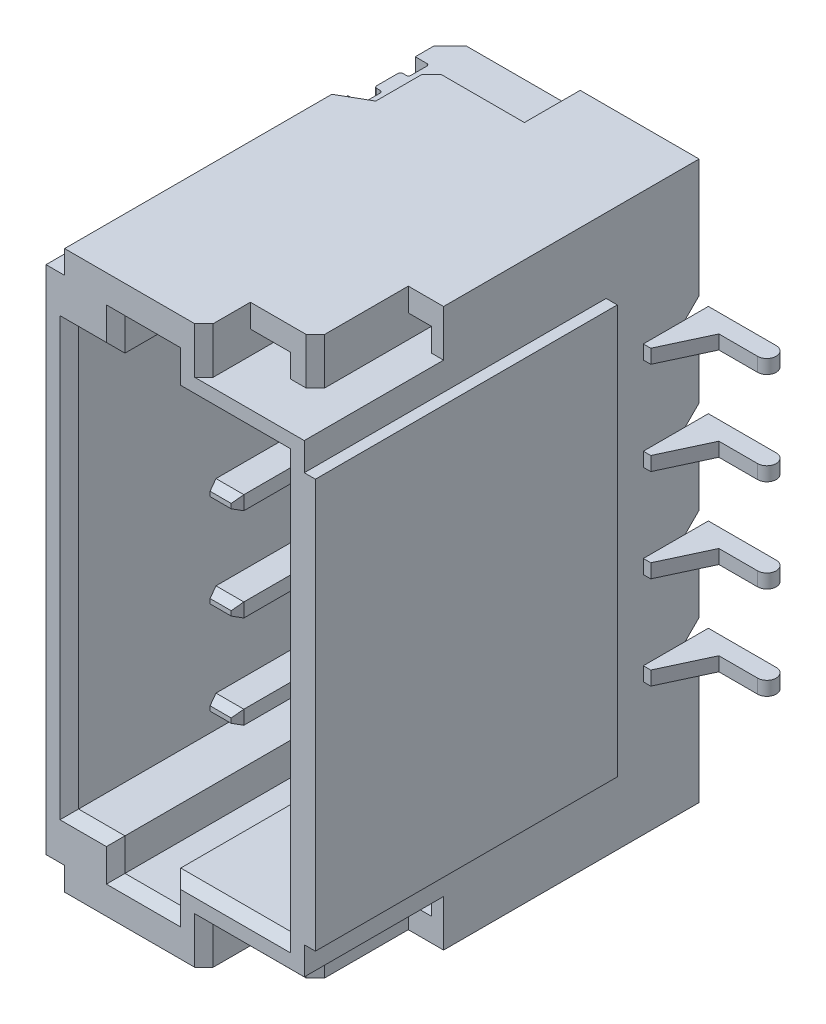
SolidWorks part; units mm, degrees
ref_plane "Front Plane" through (0, 0, 0) normal (0, 0, 1) x (1, 0, 0)
ref_plane "Top Plane" through (0, 0, 0) normal (0, 1, 0) x (1, 0, 0)
ref_plane "Right Plane" through (0, 0, 0) normal (1, 0, 0) x (0, 0, -1)
sketch "Sketch2" plane through (0, 0, 0) normal (0, 1, 0) x (1, 0, 0)
  line L0 (22.6306, -2.3603) -> (22.6306, -1.9103)
  line L1 (22.6306, -1.9103) -> (25.4106, -1.9103)
  line L2 (25.4106, -1.9103) -> (25.4106, -1.6603)
  line L3 (25.4106, -1.6603) -> (26.1406, -1.6603)
  line L4 (26.1406, -1.8603) -> (25.7238, -1.8603)
  line L5 (25.7238, -1.8603) -> (25.4906, -2.3603)
  line L6 (25.4906, -2.3603) -> (22.6306, -2.3603)
  arc A0 (26.1406, -1.8603) -> (26.1406, -1.6603) centre (26.1406, -1.7603) ccw
extrude "Boss-Extrude2" add sketch "Sketch2" along normal blind 0.15 from offset 0.815 separate body contours L6 L0 L1 L2 L3 A0 L4 L5 offset against normal yes
move or copy body "Body-Move/Copy2" bodies to move or copy 124 copy yes number of copies 1 translate (0, -1, 0)
move or copy body "Body-Move/Copy3" bodies to move or copy 124 copy yes number of copies 1 translate (0, 1, 0)
move or copy body "Body-Move/Copy4" bodies to move or copy 126 copy yes number of copies 1 translate (0, 1, 0)
sketch "Sketch3" plane through (0, 0, 0) normal (0, 1, 0) x (1, 0, 0)
  line L0 (22.7306, -2.9603) -> (24.1306, -2.9603)
  line L1 (24.1306, -2.9603) -> (24.1306, -1.8353)
  line L2 (24.1306, -1.8353) -> (23.9556, -1.6603)
  line L3 (23.9556, -1.6603) -> (22.8056, -1.6603)
  line L4 (22.8056, -1.6603) -> (22.6306, -1.8353)
  line L5 (22.6306, -1.8353) -> (22.6306, -2.0353)
  line L6 (22.6306, -2.0353) -> (22.7556, -2.0353)
  line L7 (22.7806, -2.2328) -> (22.7806, -2.0603)
  line L8 (22.6306, -2.7603) -> (22.6306, -2.8603)
  line L9 (22.6306, -2.8603) -> (22.7306, -2.9603)
  line L10 (22.6306, -2.7603) -> (22.7556, -2.7603)
  line L11 (22.7806, -2.7353) -> (22.7806, -2.5628)
  line L12 (22.7181, -2.5378) -> (22.7556, -2.5378)
  line L13 (22.6931, -2.2828) -> (22.6931, -2.5128)
  line L14 (22.7181, -2.2578) -> (22.7556, -2.2578)
  arc A0 (22.7556, -2.7603) -> (22.7806, -2.7353) centre (22.7556, -2.7353) ccw
  arc A1 (22.7806, -2.5628) -> (22.7556, -2.5378) centre (22.7556, -2.5628) ccw
  arc A2 (22.7181, -2.5378) -> (22.6931, -2.5128) centre (22.7181, -2.5128) cw
  arc A3 (22.7556, -2.0353) -> (22.7806, -2.0603) centre (22.7556, -2.0603) cw
  arc A4 (22.7556, -2.2578) -> (22.7806, -2.2328) centre (22.7556, -2.2328) ccw
  arc A5 (22.7181, -2.2578) -> (22.6931, -2.2828) centre (22.7181, -2.2828) ccw
extrude "Boss-Extrude3" add sketch "Sketch3" along normal blind 0.2 from offset 2.26 separate body contours L0 L1 L2 L3 L4 L5 L6 A3 L7 A4 L14 A5 L13 A2 L12 A1 L11 A0 L10 L8 L9
sketch "Sketch4" plane through (0, 0, 0) normal (0, 0, 1) x (1, 0, 0)
  line L0 (25.5306, -3.2409) -> (22.6306, -3.2409)
  line L1 (22.6306, -3.2409) -> (22.6306, 2.7591)
  line L2 (25.5306, 2.7591) -> (22.6306, 2.7591)
  line L3 (25.5306, -3.2409) -> (25.5306, 2.7591)
extrude "Boss-Extrude4" add sketch "Sketch4" along normal blind 4.25 from offset 1.76 separate body
sketch "Sketch5" plane through (22.6306, 0, 0) normal (-1, 0, 0) x (0, 0, 1)
  line L0 (1.7603, 1.4841) -> (1.9103, 1.3341)
  line L1 (1.9103, 1.3341) -> (2.3603, 1.3341)
  line L2 (2.3603, 1.3341) -> (2.3603, 1.1841)
  line L3 (2.3603, 1.1841) -> (1.9103, 1.1841)
  line L4 (1.9103, 1.1841) -> (1.7603, 1.0341)
  line L6 (1.7603, 1.4841) -> (1.7527, 1.4841)
  line L7 (1.7527, 1.4841) -> (1.7527, 1.0341)
  line L8 (1.7527, 1.0341) -> (1.7603, 1.0341)
extrude "Cut-Extrude2" cut sketch "Sketch5" against normal through all
pattern_linear "LPattern1" count 4 spacing 1 along (0, -1, 0) of "Cut-Extrude2"
sketch "Sketch6" plane through (25.5306, 0, 0) normal (1, 0, 0) x (0, 0, -1)
  line L0 (-2.7603, -2.4409) -> (-2.7603, 1.9591)
  line L1 (-2.7603, 1.9591) -> (-6.161, 1.9591)
  line L2 (-6.161, 1.9591) -> (-6.161, -2.4409)
  line L3 (-6.161, -2.4409) -> (-2.7603, -2.4409)
extrude "Cut-Extrude3" cut sketch "Sketch6" against normal blind 0.12 flip side to cut
sketch "Sketch7" plane through (0, 0, 6.01) normal (0, 0, 1) x (1, 0, 0)
  line L0 (22.8806, -2.4909) -> (25.1606, -2.4909)
  line L1 (25.1606, -2.4909) -> (25.1606, 2.0091)
  line L2 (25.1606, 2.0091) -> (22.8806, 2.0091)
  line L3 (22.8806, 2.0091) -> (22.8806, -2.4909)
extrude "Cut-Extrude4" cut sketch "Sketch7" against normal blind 3.2
sketch "Sketch8" plane through (0, 0, 6.01) normal (0, 0, 1) x (1, 0, 0)
  line L0 (23.3806, 2.0091) -> (23.9806, 2.0091)
  line L1 (23.9806, 2.0091) -> (23.9806, 2.3591)
  line L2 (23.9806, 2.3591) -> (23.3806, 2.3591)
  line L3 (23.3806, 2.3591) -> (23.3806, 2.0091)
  line L4 (23.3806, -2.4909) -> (23.9806, -2.4909)
  line L5 (23.9806, -2.4909) -> (23.9806, -2.8409)
  line L6 (23.9806, -2.8409) -> (23.3806, -2.8409)
  line L7 (23.3806, -2.8409) -> (23.3806, -2.4909)
extrude "Cut-Extrude6" cut sketch "Sketch8" against normal blind 2.6
chamfer "Chamfer1" distance 0.1 angle 45 12 edges at (22.8806, -0.2409, 6.01) (23.1306, -2.4909, 6.01) (23.3806, -2.6659, 6.01) (23.6806, -2.8409, 6.01) (23.9806, -2.6659, 6.01) (24.5706, -2.4909, 6.01) (25.1606, -0.2409, 6.01) (24.5706, 2.0091, 6.01) (23.9806, 2.1841, 6.01) (23.6806, 2.3591, 6.01) (23.3806, 2.1841, 6.01) (23.1306, 2.0091, 6.01)
sketch "Sketch9" plane through (0, 0, 0) normal (0, 1, 0) x (1, 0, 0)
  line L0 (23.3606, -2.8103) -> (23.6606, -2.8103)
  line L1 (23.6606, -2.8103) -> (23.6606, -4.9103)
  line L2 (23.6606, -4.9103) -> (23.6242, -5.0103)
  line L3 (23.6242, -5.0103) -> (23.397, -5.0103)
  line L4 (23.397, -5.0103) -> (23.3606, -4.9103)
  line L5 (23.3606, -4.9103) -> (23.3606, -2.8103)
extrude "Boss-Extrude5" add sketch "Sketch9" along normal blind 0.15 from offset 1.82 separate body offset against normal yes
chamfer "Chamfer2" distance 0.1 distance2 0.05 1 edges at (23.5106, -1.82, 5.0103)
chamfer "Chamfer3" distance 0.05 distance2 0.1 1 edges at (23.5106, -1.67, 5.0103)
pattern_linear "LPattern2" count 4 spacing 1 along (0, 1, 0) of bodies 135
sketch "Sketch10" plane through (22.6306, 0, 0) normal (-1, 0, 0) x (0, 0, 1)
  line L0 (6.0103, 2.5091) -> (6.0103, 2.7591)
  line L1 (6.0103, 2.7591) -> (1.4717, 2.7591)
  line L2 (1.4717, 2.7591) -> (1.4717, 2.5091)
  line L3 (1.4717, 2.5091) -> (6.0103, 2.5091)
  line L4 (6.0103, -3.2409) -> (6.0103, -2.9909)
  line L5 (6.0103, -2.9909) -> (1.2054, -2.9909)
  line L6 (1.2054, -2.9909) -> (1.2054, -3.2409)
  line L7 (1.2054, -3.2409) -> (6.0103, -3.2409)
extrude "Cut-Extrude7" cut sketch "Sketch10" against normal blind 0.2
sketch "Sketch11" plane through (0, -3.2409, 0) normal (0, -1, 0) x (1, 0, 0)
  line L0 (22.6306, 3.249) -> (23.1306, 2.9603)
  line L1 (23.1306, 2.9603) -> (23.1306, 2.3603)
  line L2 (23.1306, 2.3603) -> (24.1306, 2.3603)
  line L3 (24.1306, 2.3603) -> (24.1306, 1.6436)
  line L4 (24.1306, 1.6436) -> (22.6306, 1.6436)
  line L5 (22.6306, 1.6436) -> (22.6306, 3.249)
extrude "Cut-Extrude8" cut sketch "Sketch11" against normal blind 0.5
sketch "Sketch12" plane through (23.1306, 0, 0) normal (-1, 0, 0) x (0, 0, 1)
  line L0 (2.9603, -2.9909) -> (2.9603, -2.7409)
  line L1 (2.9603, -2.7409) -> (2.9603, -3.2409) construction
  line L2 (2.9603, -2.7409) -> (2.3603, -2.7409)
  line L3 (2.3603, -2.7409) -> (2.3603, -2.9909)
  line L4 (2.3603, -2.7409) -> (2.3603, -3.2409) construction
  line L5 (2.3603, -2.9909) -> (2.9603, -2.9909)
extrude "Cut-Extrude9" cut sketch "Sketch12" against normal up to surface (1 mm away) up to face at (24.1306, -2.9909, 2.0601)
chamfer "Chamfer4" distance 0.1 angle 45 1 edges at (22.6306, -2.7409, 2.5045)
chamfer "Chamfer5" distance 0.1 angle 45 1 edges at (23.1306, -3.1159, 2.3603)
ref_plane "Plane1" through (0, -0.2409, 0) normal (0, -1, 0) x (-1, 0, 0)
mirror "Mirror1" about plane through (0, -0.2409, 0) normal (0, -1, 0) of "Chamfer5", "Cut-Extrude8", "Chamfer4", "Cut-Extrude9"
mirror "Mirror2" about plane through (0, -0.2409, 0) normal (0, -1, 0) of bodies 128
sketch "Sketch13" plane through (0, -3.2409, 0) normal (0, -1, 0) x (1, 0, 0)
  line L0 (24.3306, 5.5103) -> (24.3306, 6.0696)
  line L1 (25.0306, 4.5103) -> (25.671, 4.5103)
  line L2 (25.0306, 4.5103) -> (25.0306, 5.5103)
  line L3 (24.3306, 5.5103) -> (25.0306, 5.5103)
  line L4 (25.671, 4.5103) -> (25.671, 6.0696)
  line L5 (25.671, 6.0696) -> (24.3306, 6.0696)
  point P0 (24.3306, 5.5103)
  point P1 (25.0306, 4.5103)
  point P8 (25.0306, 5.4103)
extrude "Cut-Extrude10" cut sketch "Sketch13" against normal blind 0.5
chamfer "Chamfer6" distance 0.1 angle 45 2 edges at (24.3306, -2.9909, 6.01) (25.0306, -2.9909, 5.5103)
sketch "Sketch14" plane through (0, 0, 5.5103) normal (0, 0, 1) x (1, 0, 0)
  line L0 (24.3306, -2.7409) -> (24.3306, -2.9909)
  line L1 (24.3306, -2.7409) -> (24.3306, -3.2409) construction
  line L2 (24.3306, -2.9909) -> (24.7617, -2.9909)
  line L3 (24.7617, -2.9909) -> (24.7617, -2.7409)
  line L4 (24.3306, -2.7409) -> (24.9306, -2.7409) construction
  line L5 (24.7617, -2.7409) -> (24.3306, -2.7409)
  line L6 (25.0306, -2.7409) -> (25.0306, -2.9909)
  line L7 (25.0306, -2.7409) -> (25.0306, -3.2409) construction
  line L8 (25.0306, -2.9909) -> (25.2818, -2.9909)
  line L9 (25.2818, -2.9909) -> (25.2818, -2.7409)
  line L10 (25.0306, -2.7409) -> (25.4106, -2.7409) construction
  line L11 (25.2818, -2.7409) -> (25.0306, -2.7409)
extrude "Cut-Extrude11" cut sketch "Sketch14" against normal blind 2
mirror "Mirror3" about plane through (0, -0.2409, 0) normal (0, -1, 0) of "Chamfer6", "Cut-Extrude10", "Cut-Extrude11"
